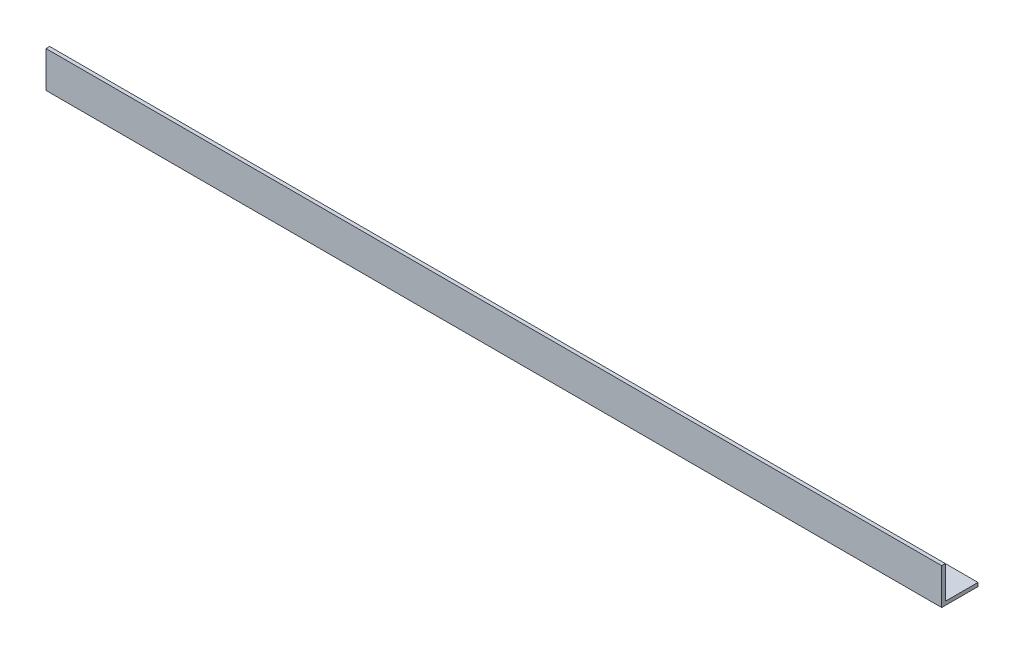
SolidWorks part; units mm, degrees
ref_plane "Спереди" through (0, 0, 0) normal (0, 0, 1) x (1, 0, 0)
ref_plane "Сверху" through (0, 0, 0) normal (0, 1, 0) x (1, 0, 0)
ref_plane "Справа" through (0, 0, 0) normal (1, 0, 0) x (0, 0, -1)
sketch "Эскиз1" plane through (0, 0, 0) normal (1, 0, 0) x (0, 0, -1)
  line L0 (0, 0) -> (0, 15)
  line L1 (0, 15) -> (1.5, 15)
  line L2 (1.5, 15) -> (1.5, 1.5)
  line L3 (1.5, 1.5) -> (15, 1.5)
  line L4 (15, 1.5) -> (15, 0)
  line L5 (15, 0) -> (0, 0)
  dimension "D1" = 15
  dimension "D2" = 15
  dimension "D3" = 1.5
  dimension "D4" = 1.5
extrude "Бобышка-Вытянуть1" add sketch "Эскиз1" along normal blind 370
